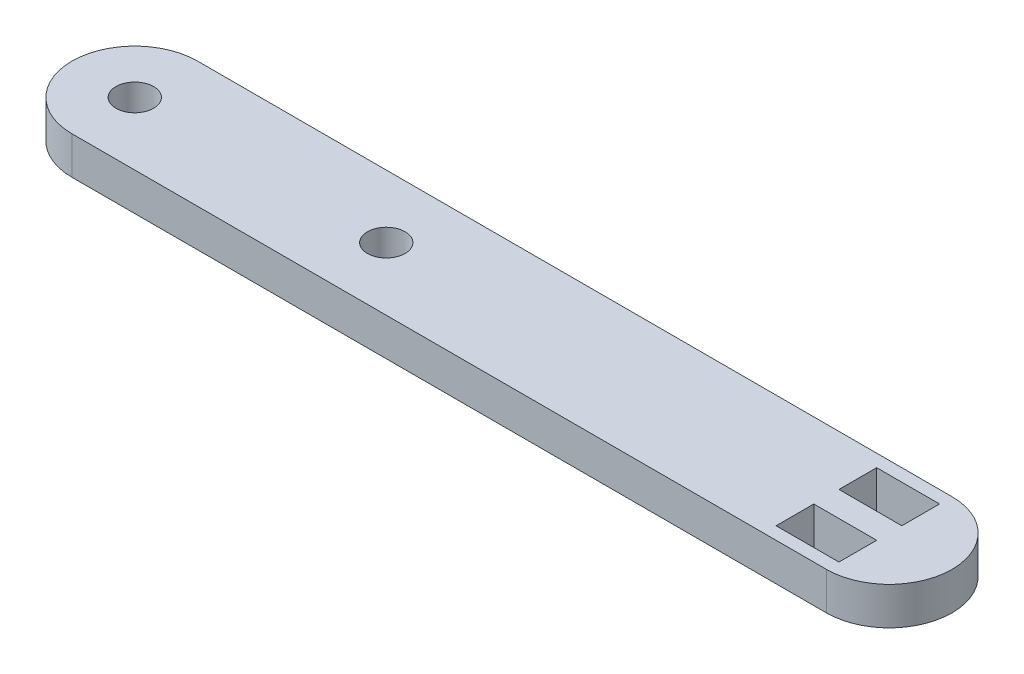
SolidWorks part; units mm, degrees
ref_plane "Front Plane" through (0, 0, 0) normal (0, 0, 1) x (1, 0, 0)
ref_plane "Top Plane" through (0, 0, 0) normal (0, 1, 0) x (1, 0, 0)
ref_plane "Right Plane" through (0, 0, 0) normal (1, 0, 0) x (0, 0, -1)
sketch "Sketch1" plane through (0, 0, 0) normal (0, 1, 0) x (1, 0, 0)
  line L0 (-30, 10) -> (-30, 0) construction
  line L1 (0, 0) -> (-60, 0)
  line L3 (0, 10) -> (-60, 10)
  line L5 (-65, 5) -> (-21.5, 5) construction
  line L6 (0, 1) -> (-5, 1)
  line L7 (0, 6) -> (-5, 6)
  line L8 (0, 6) -> (0, 9)
  line L9 (0, 9) -> (-5, 9)
  line L10 (-5, 6) -> (-5, 9)
  line L11 (-5, 4) -> (-5, 1)
  line L12 (0, 4) -> (-5, 4)
  line L13 (0, 4) -> (0, 1)
  arc A0 (-60, 10) -> (-60, 0) centre (-60, 5) ccw
  arc A1 (0, 10) -> (0, 0) centre (0, 5) cw
  circle A2 centre (-60, 5) radius 1.5
  circle A4 centre (-40, 5) radius 1.5
  dimension "D3" = 10
  dimension "D4" = 3
  dimension "D5" = 3
  dimension "D6" = 3
  dimension "D1" = 10
  dimension "D2" = 60
  dimension "D7" = 20
  dimension "D8" = 6
  dimension "D9" = 5
extrude "Boss-Extrude1" add sketch "Sketch1" along normal blind 3
